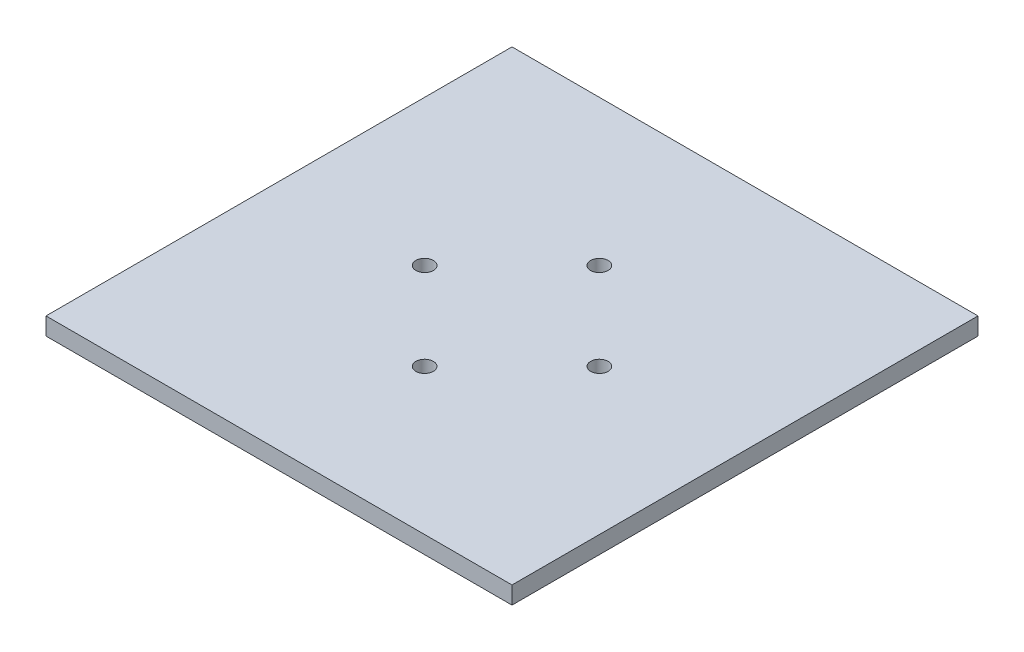
SolidWorks part; units mm, degrees
ref_plane "前视基准面" through (0, 0, 0) normal (0, 0, 1) x (1, 0, 0)
ref_plane "上视基准面" through (0, 0, 0) normal (0, 1, 0) x (1, 0, 0)
ref_plane "右视基准面" through (0, 0, 0) normal (1, 0, 0) x (0, 0, -1)
sketch "草图1" plane through (0, 0, 0) normal (0, 1, 0) x (1, 0, 0)
  line L1 (-40, -40) -> (40, -40)
  line L2 (-40, -40) -> (-40, 40)
  line L3 (-40, 40) -> (40, 40)
  line L4 (40, -40) -> (40, 40)
  line L5 (-40, -40) -> (40, 40) construction
  line L6 (-40, 40) -> (40, -40) construction
  circle A0 centre (0, 0) radius 15 construction
  circle A1 centre (0, 15) radius 1.5
  circle A2 centre (15, 0) radius 1.5
  circle A3 centre (0, -15) radius 1.5
  circle A4 centre (-15, 0) radius 1.5
  point P0 (0, 0)
  point P18 (0, 0)
  dimension "D3" = 30
  dimension "D4" = 3
  dimension "D1" = 80
  dimension "D2" = 80
  dimension "D5" = 4
extrude "凸台-拉伸1" add sketch "草图1" along normal blind 3
